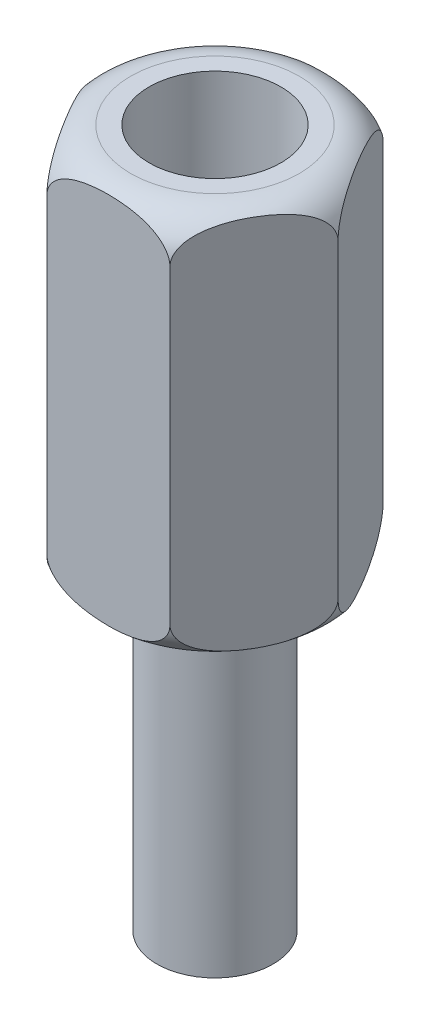
SolidWorks part; units mm, degrees
material "Brass"
ref_plane "Front Plane" through (0, 0, 0) normal (0, 0, 1) x (1, 0, 0)
ref_plane "Top Plane" through (0, 0, 0) normal (0, 1, 0) x (1, 0, 0)
ref_plane "Right Plane" through (0, 0, 0) normal (1, 0, 0) x (0, 0, -1)
sketch "Sketch1" plane through (0, 0, 0) normal (0, 1, 0) x (1, 0, 0)
  line L1 (3.1754, 0) -> (1.5877, 2.75)
  line L2 (1.5877, 2.75) -> (-1.5877, 2.75)
  line L3 (-1.5877, 2.75) -> (-3.1754, 0)
  line L4 (-3.1754, 0) -> (-1.5877, -2.75)
  line L5 (-1.5877, -2.75) -> (1.5877, -2.75)
  line L6 (1.5877, -2.75) -> (3.1754, 0)
  circle A0 centre (0, 0) radius 2.75 construction
  point P1 (0, 0)
  dimension "D1" = 5.5
extrude "Boss-Extrude1" add sketch "Sketch1" along normal blind 10
hole_wizard "M3 Clearance Hole1" positions "Sketch3" profile "Sketch2" hole size "M3" standard "ISO"
sketch "Sketch3" plane through (0, 10, 0) normal (0, 1, 0) x (-1, 0, 0)
  point P0 (0, 0)
sketch "Sketch2" plane through (0, 10, 0) normal (1, 0, 0) x (0, 0, 1)
  line L0 (0, 0) -> (0, 13.0215)
  line L1 (0, 13.0215) -> (1.7, 12)
  line L2 (1.7, 12) -> (1.7, 0)
  line L5 (1.7, 0) -> (0, 0)
  line L10 (0, 13.0215) -> (-1.7, 12) construction
  line L11 (0, -6.35) -> (0, 107.95) construction
  dimension "Hole Dia." = 3.4
  dimension "Hole Depth" = 12
  dimension "Drill Angle" = 118
sketch "Sketch4" plane through (0, 0, 0) normal (0, 0, 1) x (1, 0, 0)
  line L0 (-3.1754, 10) -> (-3.1754, 0) construction
  line L1 (-3.1754, 10) -> (-1.5877, 10) construction
  line L4 (-3.1754, 0) -> (-1.5877, 0) construction
  line L6 (-2.1754, 10) -> (-3.1754, 10)
  line L7 (-3.1754, 10) -> (-3.1754, 9)
  line L8 (-3.1754, 1) -> (-3.1754, 0)
  line L9 (-3.1754, 0) -> (-2.1754, 0)
  line L14 (0, 10) -> (0, 0) construction
  line L15 (-1.5877, 10) -> (1.5877, 10) construction
  arc A0 (-3.1754, 9) -> (-2.1754, 10) centre (-2.1754, 9) cw
  arc A2 (-3.1754, 1) -> (-2.1754, 0) centre (-2.1754, 1) ccw
  dimension "D1" = 1
revolve "Cut-Revolve1" cut sketch "Sketch4" angle 360 about L14
sketch "Sketch5" plane through (0, 0, 0) normal (0, -1, 0) x (1, 0, 0)
  circle A0 centre (0, 0) radius 1.5
  dimension "D1" = 3
extrude "Boss-Extrude2" add sketch "Sketch5" along normal blind 8
